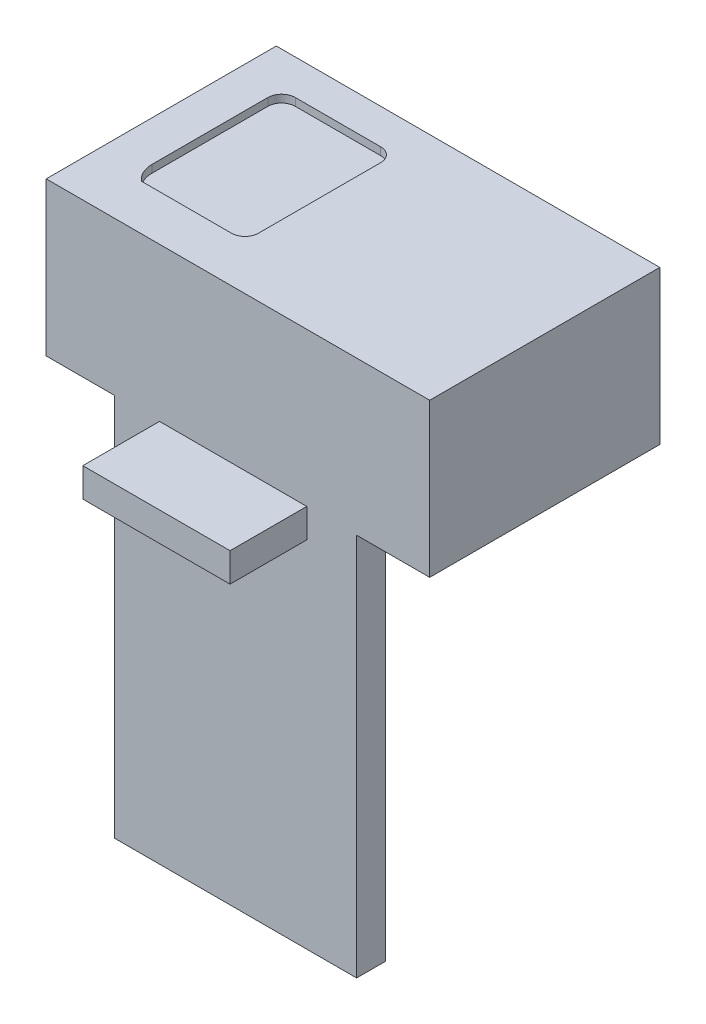
SolidWorks part; units mm, degrees
ref_plane "Alzado" through (0, 0, 0) normal (0, 0, 1) x (1, 0, 0)
ref_plane "Planta" through (0, 0, 0) normal (0, 1, 0) x (1, 0, 0)
ref_plane "Vista lateral" through (0, 0, 0) normal (1, 0, 0) x (0, 0, -1)
sketch "Croquis1" plane through (0, 0, 0) normal (0, 1, 0) x (1, 0, 0)
  line L0 (-14.7204, 15) -> (-14.7204, -15) construction
  line L1 (-25, 15) -> (25, 15)
  line L2 (-25, 15) -> (-25, -15)
  line L3 (-25, -15) -> (25, -15)
  line L4 (25, 15) -> (25, -15)
  line L5 (-25, 15) -> (25, -15) construction
  line L6 (-25, -15) -> (25, 15) construction
  line L7 (0, 0) -> (-25, 0) construction
  point P0 (0, 0)
  dimension "D1" = 50
  dimension "D2" = 30
extrude "Saliente-Extruir1" add sketch "Croquis1" along normal blind 20
sketch "Croquis2" plane through (0, 20, 0) normal (0, 1, 0) x (1, 0, 0)
  line L1 (-17.9509, 10.4241) -> (-6.8104, 10.4241)
  line L2 (-19.7375, 8.6375) -> (-19.7375, -6.4606)
  line L3 (-18.5102, -9.0612) -> (-6.791, -9.0612)
  line L4 (-5.0237, 8.6375) -> (-5.0237, -7.2939)
  arc A0 (-6.8104, 10.4241) -> (-5.0237, 8.6375) centre (-6.8104, 8.6375) cw
  arc A1 (-17.9509, 10.4241) -> (-19.7375, 8.6375) centre (-17.9509, 8.6375) ccw
  arc A2 (-5.0237, -7.2939) -> (-6.791, -9.0612) centre (-6.791, -7.2939) cw
  arc A3 (-19.7375, -6.4606) -> (-18.5102, -9.0612) centre (-16.3686, -6.4606) ccw
extrude "Cortar-Extruir1" cut sketch "Croquis2" against normal blind 1
sketch "Croquis3" plane through (0, 0, 0) normal (0, -1, 0) x (1, 0, 0)
  line L0 (-25, 15) -> (25, 15) construction
  line L1 (15.4711, 11.2619) -> (-16.0662, 11.2619)
  line L2 (15.4711, 11.2619) -> (15.4711, 15)
  line L3 (15.4711, 15) -> (-16.0662, 15)
  line L4 (-16.0662, 11.2619) -> (-16.0662, 15)
extrude "Saliente-Extruir2" add sketch "Croquis3" along normal blind 50
sketch "Croquis4" plane through (0, 0, 15) normal (0, 0, 1) x (1, 0, 0)
  line L1 (-10.2277, 0) -> (8.9721, 0)
  line L2 (-10.2277, 0) -> (-10.2277, -3.7784)
  line L3 (-10.2277, -3.7784) -> (8.9721, -3.7784)
  line L4 (8.9721, 0) -> (8.9721, -3.7784)
extrude "Saliente-Extruir3" add sketch "Croquis4" along normal blind 10
